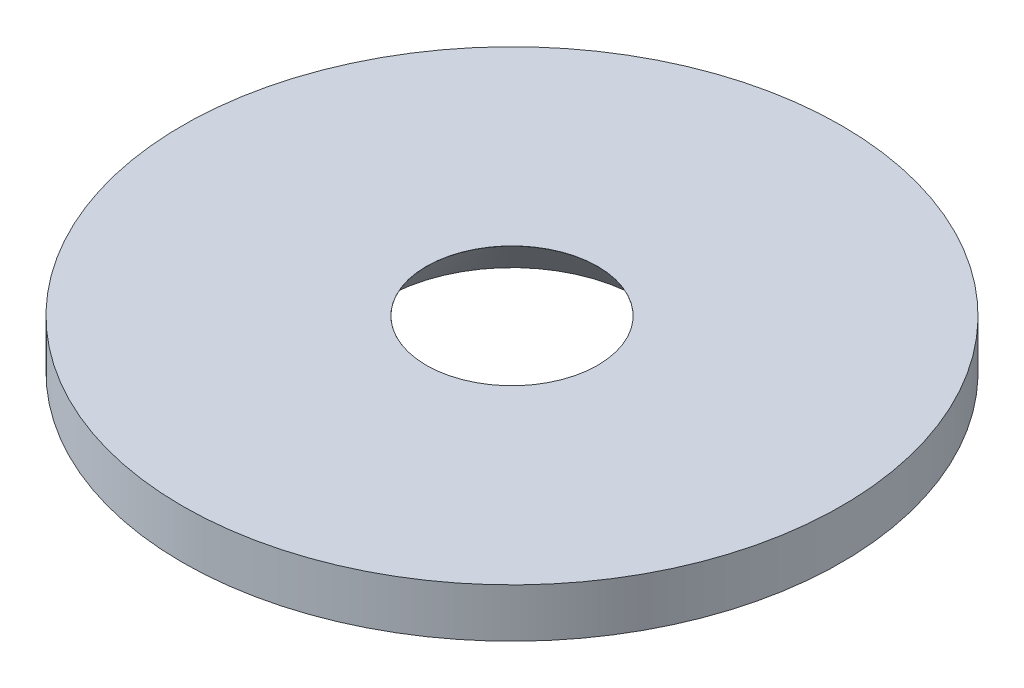
SolidWorks part; units mm, degrees
material "6061 Alloy"
ref_plane "Front Plane" through (0, 0, 0) normal (0, 0, 1) x (1, 0, 0)
ref_plane "Top Plane" through (0, 0, 0) normal (0, 1, 0) x (1, 0, 0)
ref_plane "Right Plane" through (0, 0, 0) normal (1, 0, 0) x (0, 0, -1)
sketch "Sketch1" plane through (0, 0, 0) normal (0, 1, 0) x (1, 0, 0)
  circle A0 centre (0, 0) radius 13.5
  circle A1 centre (0, 0) radius 3.51
  dimension "D1" = 27
  dimension "D2" = 7.02
extrude "Boss-Extrude1" add sketch "Sketch1" along normal blind 2
sketch "Sketch2" plane through (0, 0, 0) normal (1, 0, 0) x (0, 0, -1)
  line L0 (-3.505, 2) -> (-5.2473, 0)
  line L1 (13.5, 2) -> (-13.5, 2) construction
  line L2 (3.51, 2) -> (-3.51, 2) construction
  line L3 (-13.5, 0) -> (13.5, 0) construction
  line L4 (-5.2473, 0) -> (-3.505, 0)
  line L5 (-3.51, 0) -> (3.51, 0) construction
  line L6 (-3.505, 0) -> (-3.505, 2)
  line L7 (0, -2.0608) -> (0, 5.8713) construction
  point P8 (0, 0)
  dimension "D1" = 1.7423
  dimension "D2" = 3.505
revolve "Cut-Revolve1" cut sketch "Sketch2" angle 360 about L7
